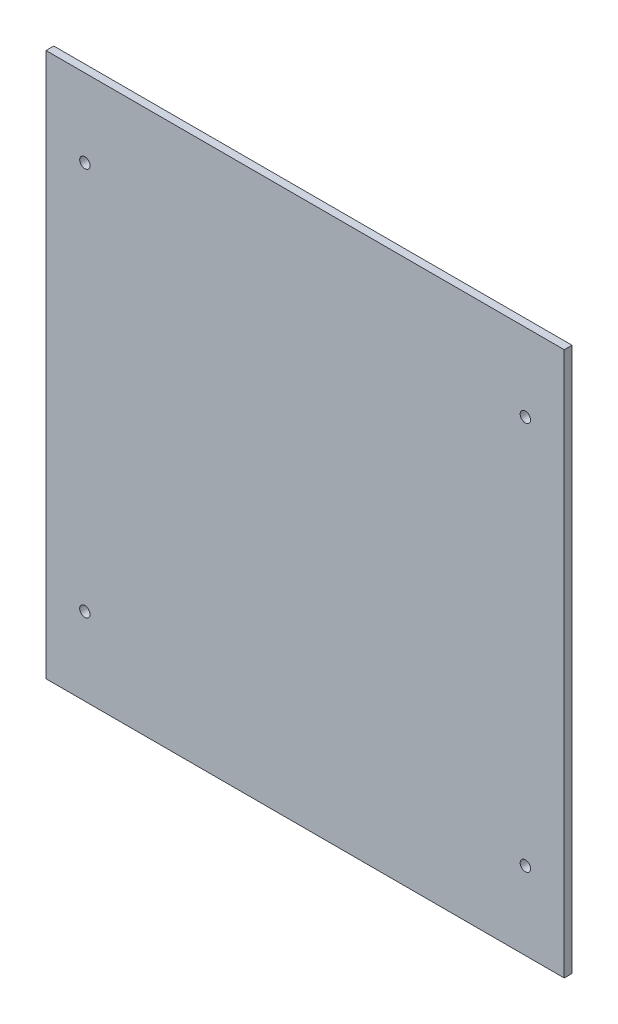
SolidWorks part; units mm, degrees
material "Acrylic (Medium-high impact)"
ref_plane "Front Plane" through (0, 0, 0) normal (0, 0, 1) x (1, 0, 0)
ref_plane "Top Plane" through (0, 0, 0) normal (0, 1, 0) x (1, 0, 0)
ref_plane "Right Plane" through (0, 0, 0) normal (1, 0, 0) x (0, 0, -1)
sketch "Sketch1" plane through (0, 0, 0) normal (0, 0, 1) x (1, 0, 0)
  line L1 (0, 0) -> (200, 0)
  line L2 (0, 0) -> (0, 210)
  line L3 (0, 210) -> (200, 210)
  line L4 (200, 0) -> (200, 210)
  dimension "D1" = 200
  dimension "D2" = 210
extrude "Boss-Extrude1" add sketch "Sketch1" along normal blind 3
sketch "Sketch2" plane through (0, 0, 0) normal (0, 0, -1) x (-1, 0, 0)
  line L0 (-200, 210) -> (0, 210) construction
  line L1 (-200, 0) -> (-200, 210) construction
  line L2 (0, 0) -> (-200, 0) construction
  line L3 (0, 210) -> (0, 0) construction
  circle A0 centre (-185, 180) radius 2
  circle A1 centre (-185, 30) radius 2
  circle A2 centre (-15, 30) radius 2
  circle A3 centre (-15, 180) radius 2
  dimension "D1" = 4
  dimension "D2" = 4
  dimension "D3" = 4
  dimension "D4" = 4
  dimension "D7" = 30
  dimension "D10" = 15
  dimension "D11" = 15
  dimension "D12" = 30
  dimension "D5" = 30
  dimension "D6" = 15
  dimension "D8" = 15
  dimension "D9" = 30
extrude "Cut-Extrude1" cut sketch "Sketch2" against normal blind 100
